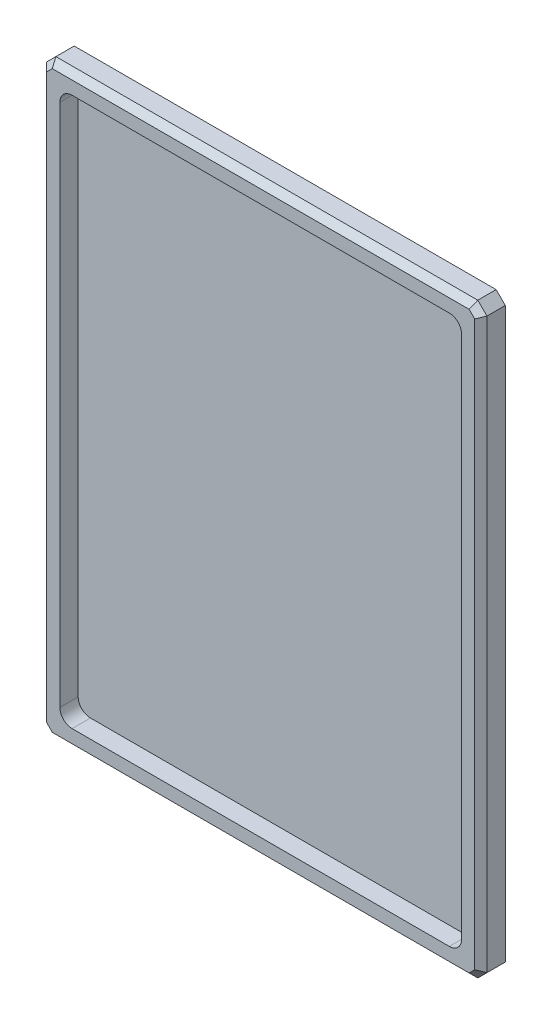
SolidWorks part; units mm, degrees
material "AISI 304"
ref_plane "Front Plane" through (0, 0, 0) normal (0, 0, 1) x (1, 0, 0)
ref_plane "Top Plane" through (0, 0, 0) normal (0, 1, 0) x (1, 0, 0)
ref_plane "Right Plane" through (0, 0, 0) normal (1, 0, 0) x (0, 0, -1)
sketch "Sketch1" plane through (0, 0, 0) normal (0, 0, 1) x (1, 0, 0)
  line L1 (114.3, -152.4) -> (-114.3, -152.4)
  line L2 (114.3, -152.4) -> (114.3, 152.4)
  line L3 (114.3, 152.4) -> (-114.3, 152.4)
  line L4 (-114.3, -152.4) -> (-114.3, 152.4)
  line L5 (114.3, -152.4) -> (-114.3, 152.4) construction
  line L6 (114.3, 152.4) -> (-114.3, -152.4) construction
  point P0 (0, 0)
  dimension "D1" = 228.6
  dimension "D2" = 304.8
extrude "Boss-Extrude1" add sketch "Sketch1" along normal blind 12.7
sketch "Sketch2" plane through (0, 0, 12.7) normal (0, 0, 1) x (1, 0, 0)
  line L0 (-114.3, 152.4) -> (-114.3, -152.4) construction
  line L1 (97.95, -142.4) -> (-97.95, -142.4)
  line L2 (104.3, -136.05) -> (104.3, 136.05)
  line L3 (97.95, 142.4) -> (-97.95, 142.4)
  line L4 (-104.3, -136.05) -> (-104.3, 136.05)
  line L5 (104.3, -142.4) -> (-104.3, 142.4) construction
  line L6 (104.3, 142.4) -> (-104.3, -142.4) construction
  line L7 (114.3, 152.4) -> (-114.3, 152.4) construction
  arc A0 (-97.95, -142.4) -> (-104.3, -136.05) centre (-97.95, -136.05) cw
  arc A1 (97.95, -142.4) -> (104.3, -136.05) centre (97.95, -136.05) ccw
  arc A2 (104.3, 136.05) -> (97.95, 142.4) centre (97.95, 136.05) ccw
  arc A3 (-97.95, 142.4) -> (-104.3, 136.05) centre (-97.95, 136.05) ccw
  point P0 (0, 0)
  dimension "D3" = 6.35
  dimension "D1" = 10
  dimension "D2" = 10
extrude "Cut-Extrude1" cut sketch "Sketch2" against normal blind 9.525
chamfer "Chamfer1" distance 4.7625 angle 45 4 edges at (-114.3, -152.4, 6.35) (114.3, -152.4, 6.35) (-114.3, 152.4, 6.35) (114.3, 152.4, 6.35)
chamfer "Chamfer2" distance 3.175 angle 45 8 edges at (-111.9188, 150.0187, 12.7) (0, 152.4, 12.7) (-114.3, 0, 12.7) (-111.9188, -150.0188, 12.7) (0, -152.4, 12.7) (111.9187, -150.0188, 12.7) (114.3, 0, 12.7) (111.9187, 150.0187, 12.7)
